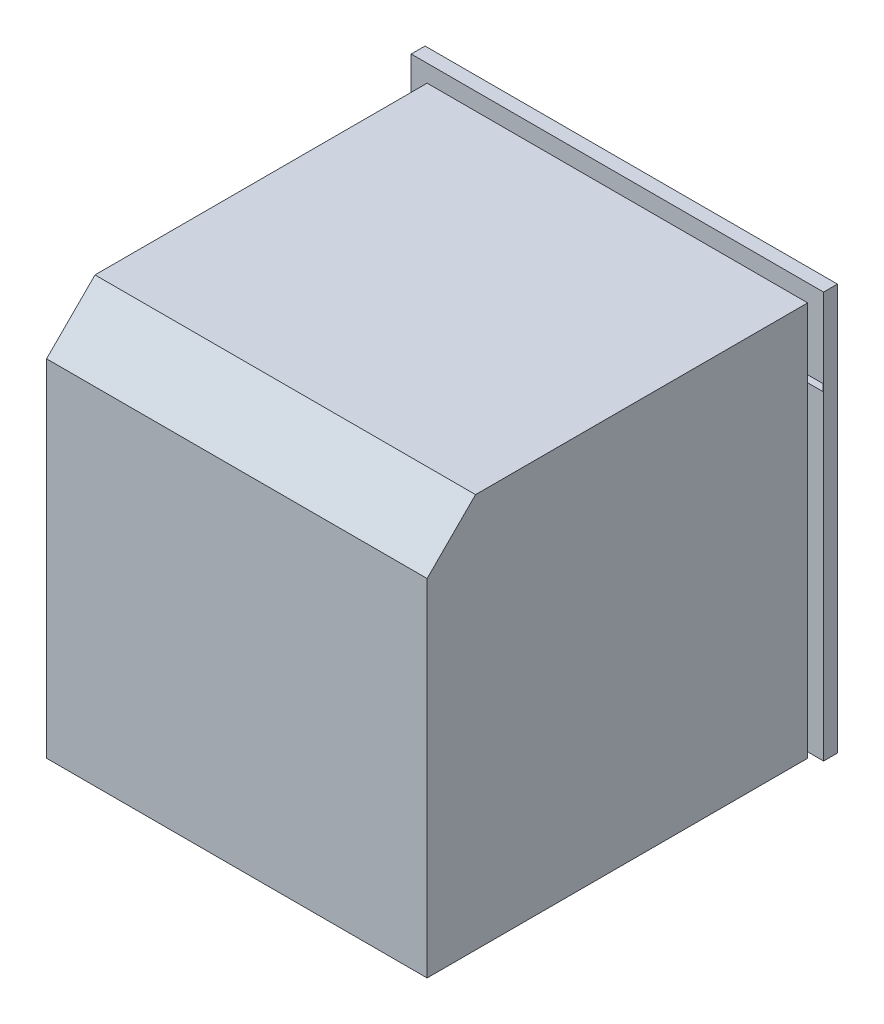
SolidWorks part; units mm, degrees
ref_plane "Front Plane" through (0, 0, 0) normal (0, 0, 1) x (1, 0, 0)
ref_plane "Top Plane" through (0, 0, 0) normal (0, 1, 0) x (1, 0, 0)
ref_plane "Right Plane" through (0, 0, 0) normal (1, 0, 0) x (0, 0, -1)
sketch "Sketch2" plane through (0, 0, 0) normal (0, 0, 1) x (1, 0, 0)
  line L1 (275, 8.708) -> (-275, 8.708)
  line L2 (275, 8.708) -> (275, 578.708)
  line L3 (275, 578.708) -> (-275, 578.708)
  line L4 (-275, 8.708) -> (-275, 578.708)
  line L5 (275, 8.708) -> (-275, 578.708) construction
  line L6 (275, 578.708) -> (-275, 8.708) construction
  point P0 (0, 293.708)
  dimension "D1" = 570
  dimension "D2" = 550
extrude "Boss-Extrude2" add sketch "Sketch2" along normal blind 550
chamfer "Chamfer1" distance 70 angle 45 1 edges at (0, 578.708, 550)
sketch "Sketch3" plane through (0, 0, 0) normal (0, 0, -1) x (-1, 0, 0)
  line L0 (275, 8.708) -> (-275, 8.708) construction
  line L1 (298, 8.708) -> (-298, 8.708)
  line L2 (298, 8.708) -> (298, 603.708)
  line L3 (298, 603.708) -> (-298, 603.708)
  line L4 (-298, 8.708) -> (-298, 603.708)
  line L5 (298, 8.708) -> (-298, 603.708) construction
  line L6 (298, 603.708) -> (-298, 8.708) construction
  point P0 (0, 306.208)
  dimension "D1" = 596
  dimension "D2" = 595
extrude "Boss-Extrude3" add sketch "Sketch3" along normal blind 20
sketch "Sketch4" plane through (0, 0, -20) normal (0, 0, -1) x (-1, 0, 0)
  line L0 (-298, 603.708) -> (-298, 8.708) construction
  line L1 (297, 60.708) -> (-298, 60.708)
  line L2 (297, 60.708) -> (297, 8.708)
  line L3 (297, 8.708) -> (-298, 8.708)
  line L4 (-298, 60.708) -> (-298, 8.708)
  line L5 (297, 60.708) -> (-298, 8.708) construction
  line L6 (297, 8.708) -> (-298, 60.708) construction
  line L7 (298, 8.708) -> (298, 603.708) construction
  line L8 (-298, 603.708) -> (298, 603.708)
  line L9 (-298, 603.708) -> (-298, 585.708)
  line L10 (-298, 585.708) -> (298, 585.708)
  line L11 (298, 603.708) -> (298, 585.708)
  point P0 (-0.5, 34.708)
  dimension "D1" = 52
  dimension "D2" = 18
extrude "Boss-Extrude4" add sketch "Sketch4" along normal blind 0.01
sketch "Sketch5" plane through (0, 0, -20.01) normal (0, 0, -1) x (-1, 0, 0)
  line L0 (297, 8.708) -> (297, 60.708) construction
  line L1 (-298, 8.708) -> (297, 8.708)
  line L2 (-298, 8.708) -> (-298, 16.708)
  line L3 (-298, 16.708) -> (297, 16.708)
  line L4 (297, 8.708) -> (297, 16.708)
  line L5 (298, 603.708) -> (-298, 603.708) construction
  line L6 (297, 478.708) -> (-297, 478.708)
  line L7 (297, 478.708) -> (297, 488.708)
  line L8 (297, 488.708) -> (-297, 488.708)
  line L9 (-297, 478.708) -> (-297, 488.708)
  dimension "D1" = 8
  dimension "D2" = 10
  dimension "D3" = 115
extrude "Cut-Extrude1" cut sketch "Sketch5" against normal blind 20.01
ref_plane "Plane1" through (0, 468.708, 0) normal (0, 1, 0) x (1, 0, 0)
sketch "Sketch7" plane through (0, 468.708, 0) normal (0, 1, 0) x (1, 0, 0)
  line L0 (-298, 20.01) -> (298, 20.01) construction
  line L1 (-209.1169, 61.3242) -> (220.8831, 61.3242)
  line L2 (-209.1169, 61.3242) -> (-209.1169, 46.3242)
  line L3 (-189.1169, 46.3242) -> (200.8831, 46.3242)
  line L4 (220.8831, 61.3242) -> (220.8831, 46.3242)
  line L6 (-209.1169, 46.3242) -> (-209.1169, 20.01)
  line L7 (-209.1169, 20.01) -> (-189.1169, 20.01)
  line L8 (-189.1169, 46.3242) -> (-189.1169, 20.01)
  line L11 (220.8831, 46.3242) -> (220.8831, 20.01)
  line L12 (220.8831, 20.01) -> (200.8831, 20.01)
  line L13 (200.8831, 46.3242) -> (200.8831, 20.01)
  dimension "D1" = 430
  dimension "D2" = 20
  dimension "D3" = 15
extrude "Boss-Extrude5" add sketch "Sketch7" against normal blind 30 separate body
